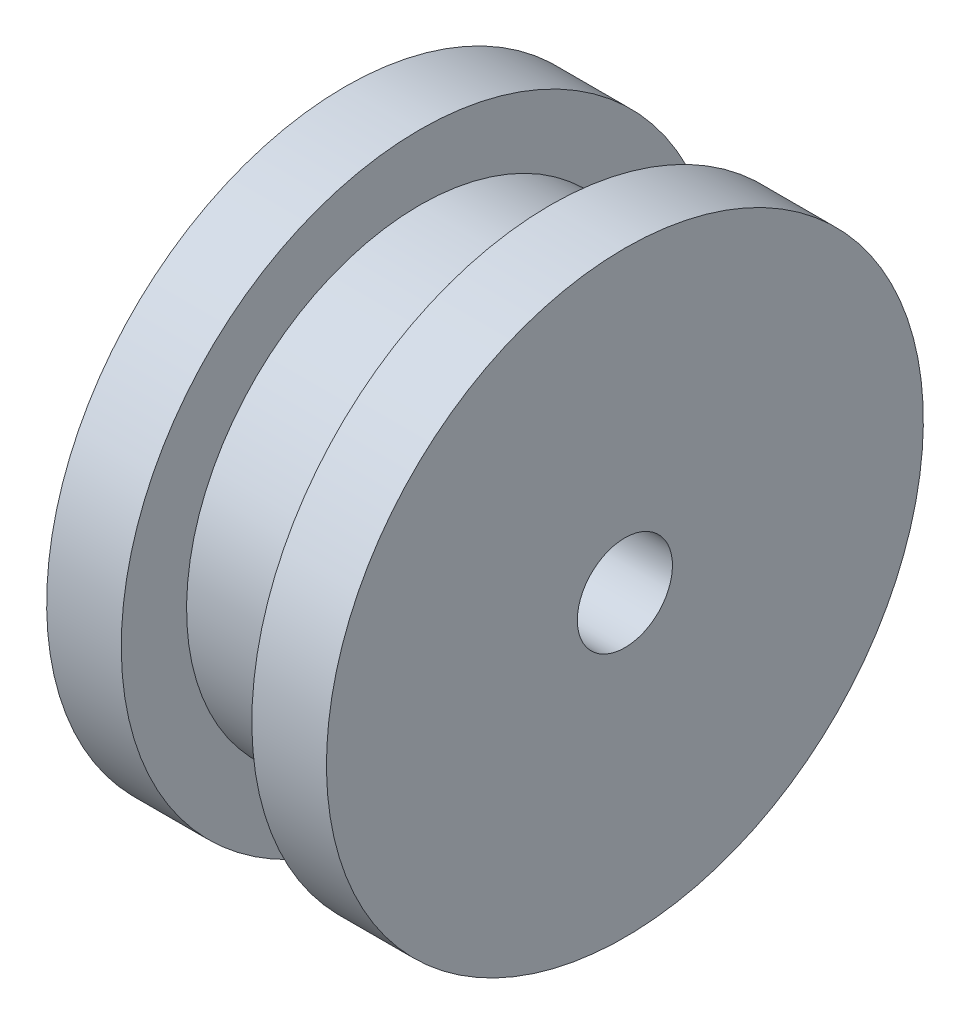
SolidWorks part; units mm, degrees
ref_plane "Front Plane" through (0, 0, 0) normal (0, 0, 1) x (1, 0, 0)
ref_plane "Top Plane" through (0, 0, 0) normal (0, 1, 0) x (1, 0, 0)
ref_plane "Right Plane" through (0, 0, 0) normal (1, 0, 0) x (0, 0, -1)
sketch "Sketch1" plane through (0, 0, 0) normal (0, 0, 1) x (1, 0, 0)
  line L0 (0, 0) -> (0, 16)
  line L2 (4, 16) -> (4, 12.5)
  line L3 (4, 12.5) -> (11, 12.5)
  line L4 (11, 12.5) -> (11, 16)
  line L6 (15, 16) -> (15, 0)
  line L7 (15, 0) -> (0, 0)
  line L10 (11, 16) -> (15, 16)
  line L11 (4, 16) -> (0, 16)
revolve "Revolve1" add sketch "Sketch1" angle 360 about L7
sketch "Sketch2" plane through (0, 0, 0) normal (-1, 0, 0) x (0, 0, 1)
  circle A0 centre (0, 0) radius 2.55
extrude "Cut-Extrude1" cut sketch "Sketch2" against normal up to surface (15 mm away) up to face at (15, 16, 0)
